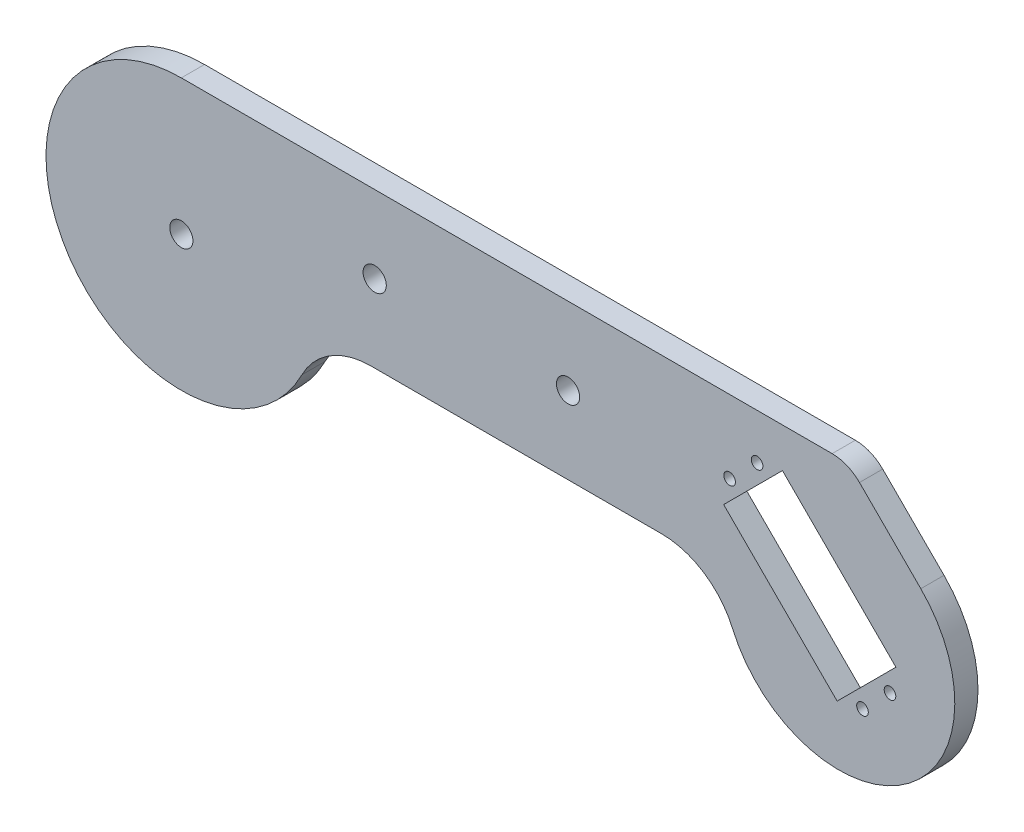
SolidWorks part; units mm, degrees
material "Beech"
ref_plane "Front Plane" through (0, 0, 0) normal (0, 0, 1) x (1, 0, 0)
ref_plane "Top Plane" through (0, 0, 0) normal (0, 1, 0) x (1, 0, 0)
ref_plane "Right Plane" through (0, 0, 0) normal (1, 0, 0) x (0, 0, -1)
sketch "Sketch1" plane through (0, 0, 0) normal (0, 0, 1) x (1, 0, 0)
  line L0 (0, 35) -> (168.2843, 35)
  line L1 (132.5955, -27.4147) -> (192.4147, 32.4045) construction
  line L2 (50, 15) -> (150, 15) construction
  line L3 (124.1742, -5) -> (48.9898, -5)
  line L4 (175.3553, 32.0711) -> (191.2132, 16.2132)
  line L6 (155.434, 24.7688) -> (184.779, -4.5762)
  line L8 (155.434, 24.7688) -> (140.2312, 9.566)
  line L10 (140.2312, 9.566) -> (169.5762, -19.779)
  line L11 (184.779, -4.5762) -> (169.5762, -19.779)
  arc A0 (0, 35) -> (31.1753, -15.9091) centre (0, 0) ccw
  arc A1 (142.5045, -17) -> (191.2132, 16.2132) centre (170, -5) ccw
  circle A2 centre (0, 0) radius 3
  circle A3 centre (50, 15) radius 3
  circle A4 centre (100, 15) radius 3
  arc A5 (124.1742, -5) -> (142.5045, -17) centre (124.1742, -25) cw
  arc A6 (48.9898, -5) -> (31.1753, -15.9091) centre (48.9898, -25) ccw
  arc A7 (175.3553, 32.0711) -> (168.2843, 35) centre (168.2843, 25) ccw
  circle A8 centre (183.241, -11.1346) radius 1.5
  circle A9 centre (176.1346, -18.241) radius 1.5
  circle A10 centre (141.7692, 16.1244) radius 1.5
  circle A11 centre (148.8756, 23.2308) radius 1.5
  point P8 (194.6466, 18.904)
  point P19 (162.5051, 2.4949)
  point P21 (140, -5)
  point P26 (162.5051, 2.4949)
  dimension "D1" = 60
  dimension "D3" = 45
  dimension "D7" = 6
  dimension "D4" = 20
  dimension "D5" = 10
  dimension "D14" = 35
  dimension "D15" = 30
  dimension "D17" = 3
  dimension "D18" = 3
  dimension "D19" = 84.5972
  dimension "D2" = 3.55
  dimension "D6" = 21.5
  dimension "D8" = 100
  dimension "D9" = 50
  dimension "D10" = 41.5
  dimension "D11" = 20
  dimension "D12" = 20
  dimension "D13" = 170
  dimension "D16" = 3.55
extrude "Boss-Extrude1" add sketch "Sketch1" along normal blind 6
